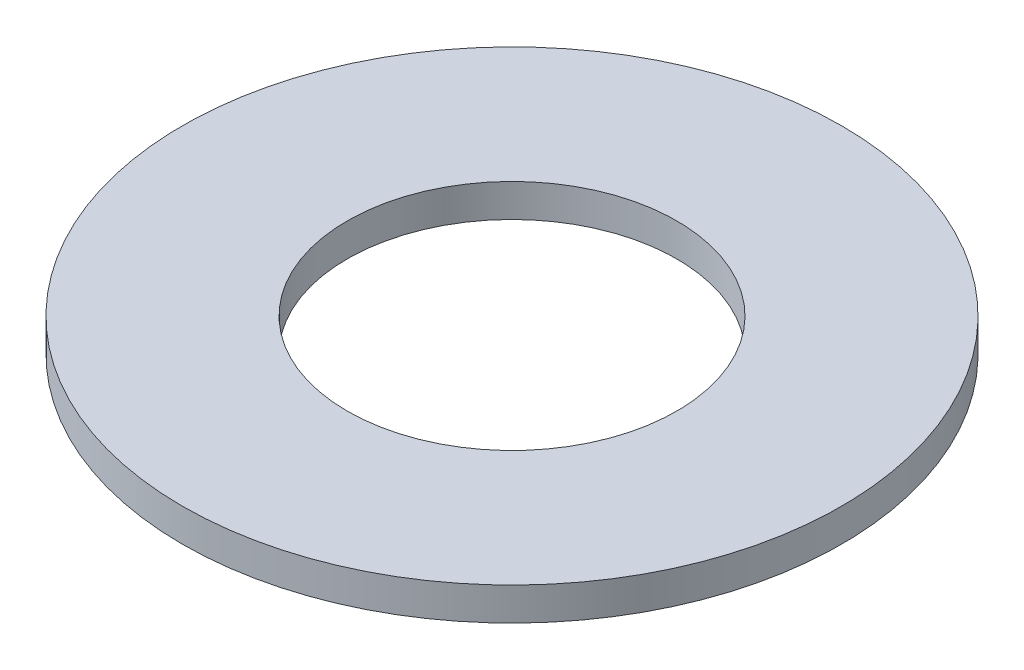
SolidWorks part; units mm, degrees
material "1060 Alloy"
ref_plane "Front Plane" through (0, 0, 0) normal (0, 0, 1) x (1, 0, 0)
ref_plane "Top Plane" through (0, 0, 0) normal (0, 1, 0) x (1, 0, 0)
ref_plane "Right Plane" through (0, 0, 0) normal (1, 0, 0) x (0, 0, -1)
sketch "Sketch1" plane through (0, 0, 0) normal (0, 1, 0) x (1, 0, 0)
  circle A2 centre (0, 0) radius 10
  circle A3 centre (0, 0) radius 5
  point P5 (0, 0)
  point P12 (0, 0)
  dimension "D2" = 10
  dimension "D3" = 20
extrude "Boss-Extrude1" add sketch "Sketch1" against normal blind 1
